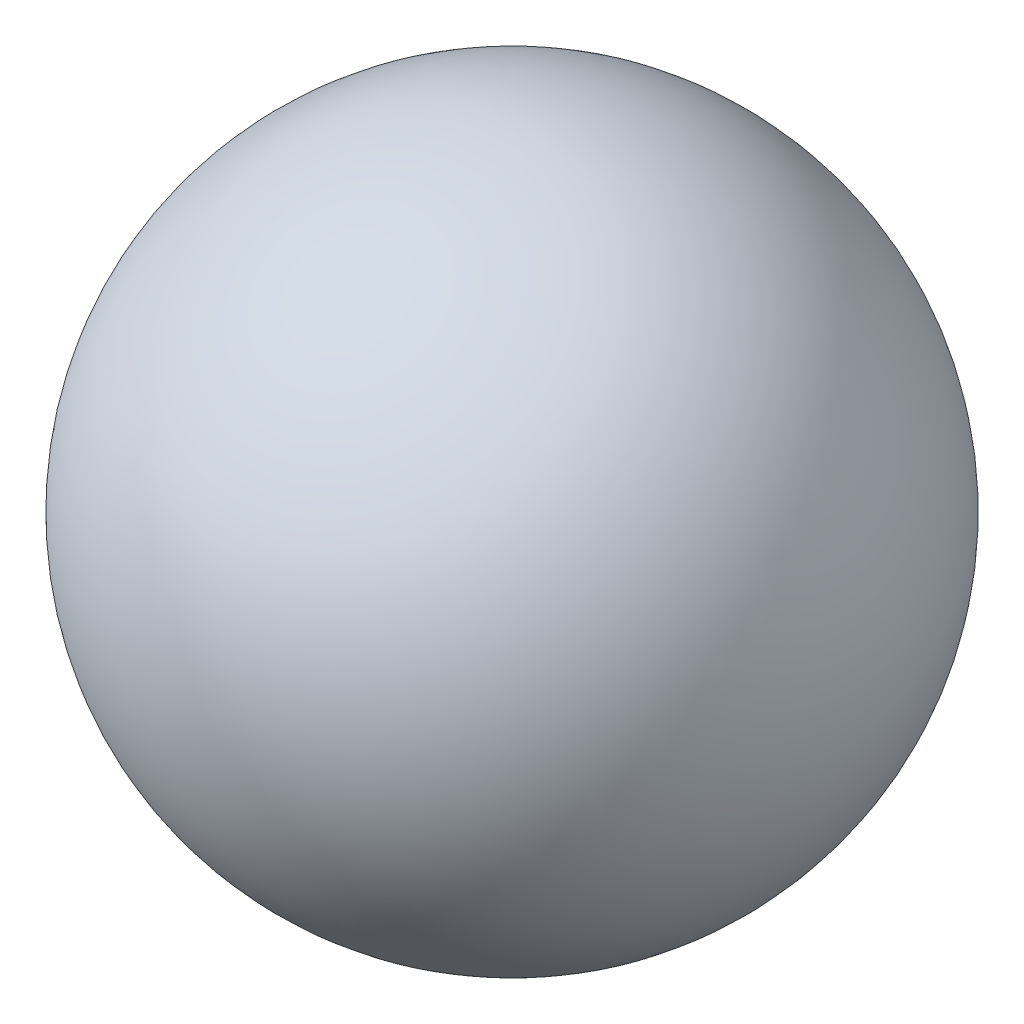
SolidWorks part; units mm, degrees
ref_plane "Ön Düzlem" through (0, 0, 0) normal (0, 0, 1) x (1, 0, 0)
ref_plane "Üst Düzlem" through (0, 0, 0) normal (0, 1, 0) x (1, 0, 0)
ref_plane "Sağ Düzlem" through (0, 0, 0) normal (1, 0, 0) x (0, 0, -1)
sketch "Sketch1" plane through (0, 0, 0) normal (0, 0, 1) x (1, 0, 0)
  line L0 (0, 87.5839) -> (0, -87.5839)
  line L1 (0, 87.5839) -> (0, -87.5839) construction
  arc A0 (0, 87.5839) -> (0, -87.5839) centre (0, 0) ccw
revolve "Revolve1" add sketch "Sketch1" angle 360 about L1
